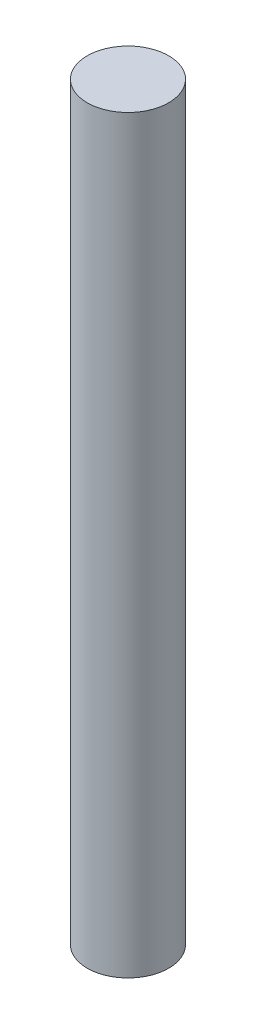
SolidWorks part; units mm, degrees
ref_plane "Front Plane" through (0, 0, 0) normal (0, 0, 1) x (1, 0, 0)
ref_plane "Top Plane" through (0, 0, 0) normal (0, 1, 0) x (1, 0, 0)
ref_plane "Right Plane" through (0, 0, 0) normal (1, 0, 0) x (0, 0, -1)
sketch "Sketch1" plane through (0, 0, 0) normal (0, 1, 0) x (1, 0, 0)
  circle A0 centre (0, 0) radius 2.5
  dimension "D1" = 5
extrude "Boss-Extrude1" add sketch "Sketch1" along normal blind 46
